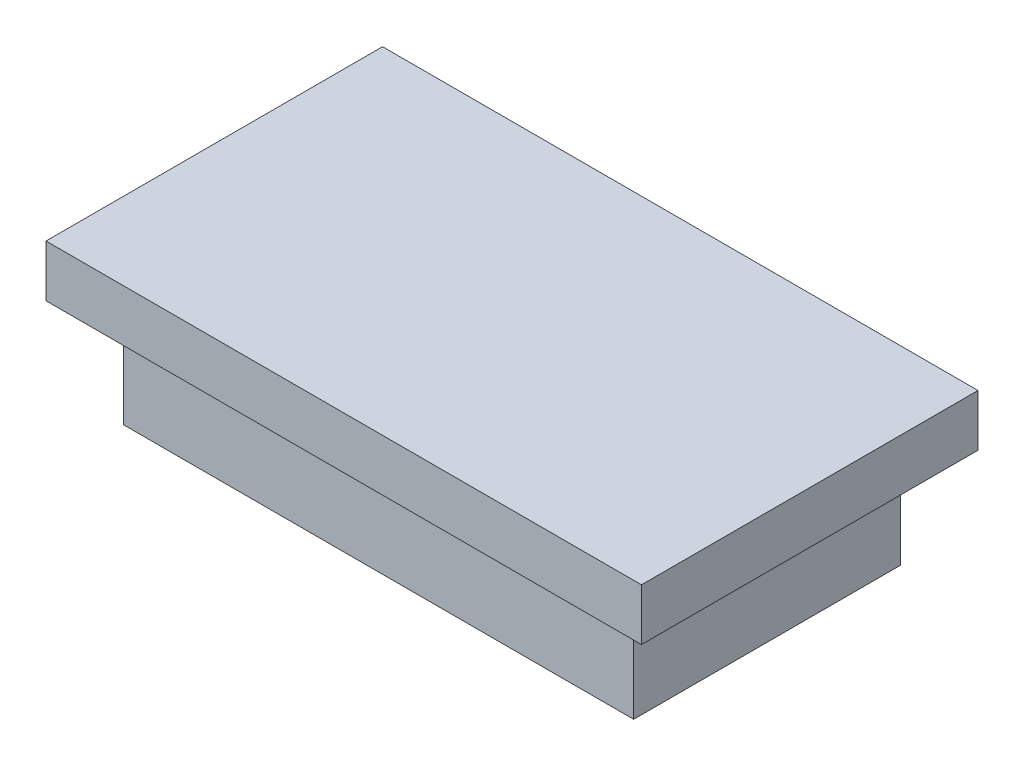
SolidWorks part; units mm, degrees
ref_plane "Спереди" through (0, 0, 0) normal (0, 0, 1) x (1, 0, 0)
ref_plane "Сверху" through (0, 0, 0) normal (0, 1, 0) x (1, 0, 0)
ref_plane "Справа" through (0, 0, 0) normal (1, 0, 0) x (0, 0, -1)
sketch "Sketch1" plane through (0, 0, 0) normal (0, 1, 0) x (1, 0, 0)
  line L1 (9.85, -5.15) -> (-9.85, -5.15)
  line L2 (9.85, -5.15) -> (9.85, 5.15)
  line L3 (9.85, 5.15) -> (-9.85, 5.15)
  line L4 (-9.85, -5.15) -> (-9.85, 5.15)
  line L5 (9.85, -5.15) -> (-9.85, 5.15) construction
  line L6 (9.85, 5.15) -> (-9.85, -5.15) construction
  point P0 (0, 0)
  dimension "D1" = 19.7
  dimension "D2" = 10.3
extrude "Boss-Extrude1" add sketch "Sketch1" along normal blind 4
sketch "Sketch2" plane through (0, 4, 0) normal (0, 1, 0) x (1, 0, 0)
  line L1 (11.5, -6.5) -> (-11.5, -6.5)
  line L2 (11.5, -6.5) -> (11.5, 6.5)
  line L3 (11.5, 6.5) -> (-11.5, 6.5)
  line L4 (-11.5, -6.5) -> (-11.5, 6.5)
  line L5 (11.5, -6.5) -> (-11.5, 6.5) construction
  line L6 (11.5, 6.5) -> (-11.5, -6.5) construction
  point P0 (0, 0)
  dimension "D1" = 13
  dimension "D2" = 23
extrude "Boss-Extrude2" add sketch "Sketch2" along normal blind 2
